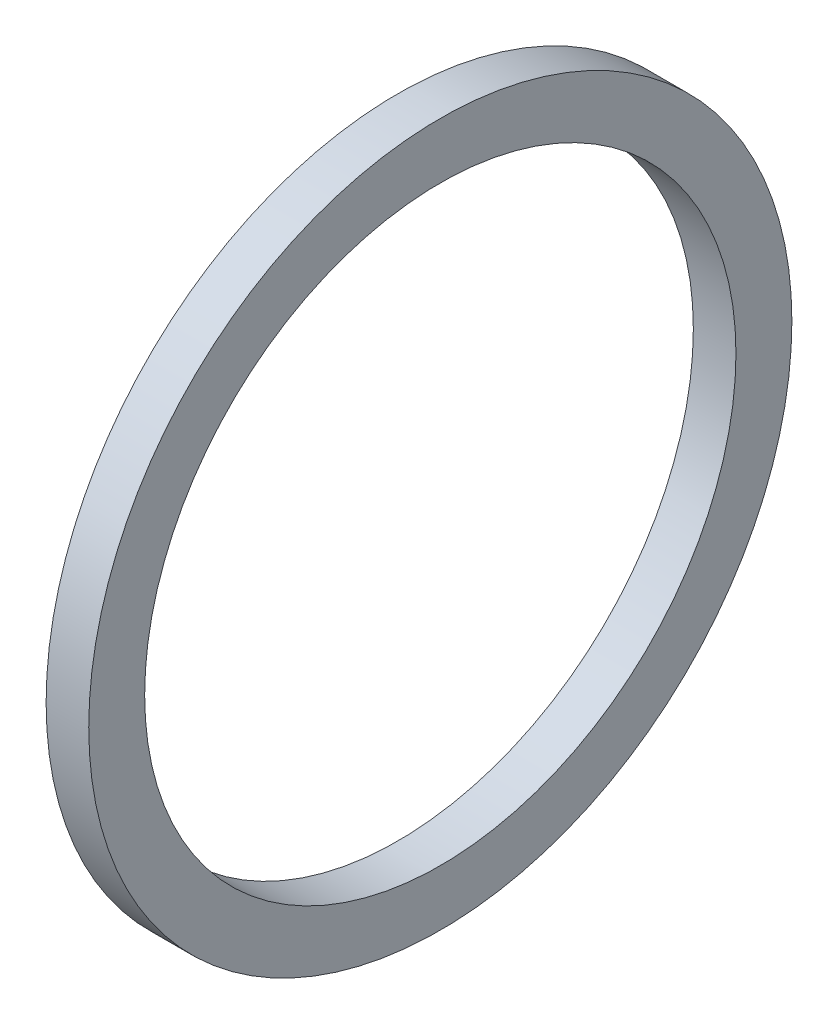
SolidWorks part; units mm, degrees
ref_plane "Front Plane" through (0, 0, 0) normal (0, 0, 1) x (1, 0, 0)
ref_plane "Top Plane" through (0, 0, 0) normal (0, 1, 0) x (1, 0, 0)
ref_plane "Right Plane" through (0, 0, 0) normal (1, 0, 0) x (0, 0, -1)
sketch "Sketch1" plane through (0, 0, 0) normal (0, 0, 1) x (1, 0, 0)
  line L0 (-43.7166, 0) -> (79.6876, 0) construction
  line L2 (0, -14.097) -> (2.032, -14.097)
  line L3 (0, -14.097) -> (0, -16.764)
  line L4 (0, -16.764) -> (2.032, -16.764)
  line L5 (2.032, -14.097) -> (2.032, -16.764)
  dimension "A" = 28.194
  dimension "B" = 33.528
  dimension "C" = 2.032
revolve "Revolve1" add sketch "Sketch1" angle 360 about L0
sketch "Sketch2" [suppressed] plane through (0, 0, 0) normal (0, 0, 1) x (1, 0, 0)
  line L0 (-34.685, 0) -> (47.6686, 0) construction
  circle A0 centre (2.54, -5.715) radius 0.762
  dimension "D1" = 2.54
  dimension "E" = 2.032
  dimension "D" = 25.908
revolve "Revolve3" [suppressed] add sketch "Sketch2" angle 360 about L0
